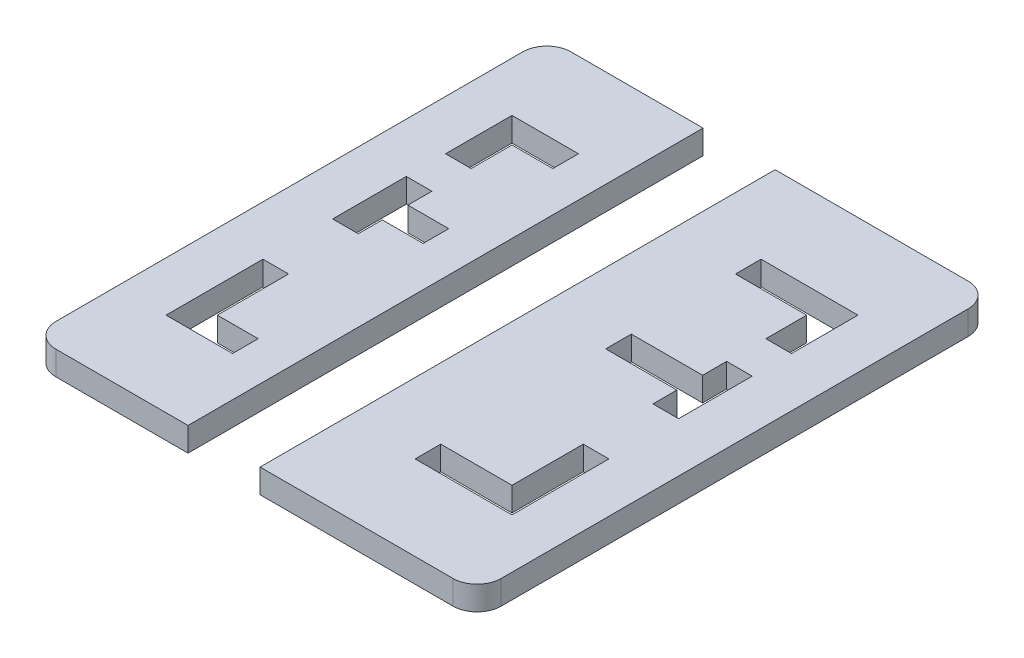
SolidWorks part; units mm, degrees
ref_plane "Front Plane" through (0, 0, 0) normal (0, 0, 1) x (1, 0, 0)
ref_plane "Top Plane" through (0, 0, 0) normal (0, 1, 0) x (1, 0, 0)
ref_plane "Right Plane" through (0, 0, 0) normal (1, 0, 0) x (0, 0, -1)
sketch "Sketch1" plane through (0, 0, 0) normal (0, 1, 0) x (1, 0, 0)
  line L0 (0.7, -32.157) -> (0.7, 32.157)
  line L1 (-28.5, -32.157) -> (28.5, -32.157) construction
  line L2 (-28.5, -32.157) -> (-28.5, 32.157) construction
  line L3 (-28.5, 32.157) -> (28.5, 32.157) construction
  line L4 (28.5, -32.157) -> (28.5, 32.157) construction
  line L5 (-8.3, 32.157) -> (-8.3, -32.157)
  line L6 (27.8, -32.157) -> (27.8, 32.157)
  line L7 (-27.8, -32.157) -> (-27.8, 32.157)
  line L8 (0, -32.157) -> (0, 32.157) construction
  line L9 (0.7, -32.157) -> (27.8, -32.157)
  line L10 (27.8, 32.157) -> (0.7, 32.157)
  line L11 (-8.3, 32.157) -> (-27.8, 32.157)
  line L12 (-8.3, -32.157) -> (-27.8, -32.157)
  line L13 (28.5, 0) -> (27.8, 0) construction
  line L14 (27.8, 20) -> (28.5, 20) construction
sketch "Sketch2" plane through (0, 0, 0) normal (0, 0, 1) x (1, 0, 0)
  line L0 (0.7, 0) -> (27.8, 0) construction
  line L1 (27.8, 0) -> (0.7, 0)
  line L2 (27.8, 0) -> (27.8, 3)
  line L3 (27.8, 3) -> (0.7, 3)
  line L4 (0.7, 0) -> (0.7, 3)
  line L5 (28.5, 3) -> (0.7, 3) construction
  line L7 (-8.3, 3) -> (-27.8, 3)
  line L8 (-8.3, 3) -> (-8.3, 0)
  line L9 (-8.3, 0) -> (-27.8, 0)
  line L10 (-27.8, 3) -> (-27.8, 0)
extrude "Boss-Extrude1" add sketch "Sketch1" along normal up to vertex (3 mm away) up to point (-27.8, 3, 0)
sketch "Sketch3" plane through (0, 0, 0) normal (0, 1, 0) x (1, 0, 0)
  line L0 (21.5, 2.3) -> (-21.5, 2.3) construction
  line L1 (21.5, -21.5) -> (-21.5, -21.5) construction
  line L2 (21.5, -21.5) -> (21.5, 21.5) construction
  line L3 (21.5, 21.5) -> (-21.5, 21.5) construction
  line L4 (-21.5, -21.5) -> (-21.5, 21.5) construction
  line L5 (18.5, -18.5) -> (-18.5, -18.5) construction
  line L6 (18.5, -18.5) -> (18.5, 18.5) construction
  line L7 (18.5, 18.5) -> (-18.5, 18.5) construction
  line L8 (-18.5, -18.5) -> (-18.5, 18.5) construction
  line L9 (-21.5, 5.3) -> (21.5, 5.3) construction
  line L10 (21.5, -0.7) -> (-21.5, -0.7) construction
  line L11 (21.5, 8.3) -> (-21.5, 8.3) construction
  line L12 (21.5, -9.6) -> (-21.5, -9.6) construction
  line L13 (21.5, 13.4) -> (-21.5, 13.4) construction
  line L14 (-13.4, -21.5) -> (-13.4, 21.5) construction
  line L15 (9.6, -21.5) -> (9.6, 21.5) construction
  line L16 (21.5, -21.5) -> (9.6, -21.5)
  line L17 (9.6, -21.5) -> (9.6, -18.5)
  line L18 (9.6, -18.5) -> (18.5, -18.5)
  line L19 (18.5, -18.5) -> (18.5, -9.6)
  line L20 (18.5, -9.6) -> (21.5, -9.6)
  line L21 (21.5, -9.6) -> (21.5, -21.5)
  line L22 (21.5, -0.7) -> (18.5, -0.7)
  line L23 (18.5, -0.7) -> (18.5, 2.3)
  line L24 (18.5, 2.3) -> (9.6, 2.3)
  line L25 (9.6, 2.3) -> (9.6, 5.3)
  line L26 (9.6, 5.3) -> (18.5, 5.3)
  line L27 (18.5, 5.3) -> (18.5, 8.3)
  line L28 (18.5, 8.3) -> (21.5, 8.3)
  line L29 (21.5, 8.3) -> (21.5, -0.7)
  line L30 (21.5, 13.4) -> (18.5, 13.4)
  line L31 (18.5, 13.4) -> (18.5, 18.5)
  line L32 (18.5, 18.5) -> (9.6, 18.5)
  line L33 (9.6, 18.5) -> (9.6, 21.5)
  line L34 (9.6, 21.5) -> (21.5, 21.5)
  line L35 (21.5, 21.5) -> (21.5, 13.4)
  line L36 (-13.4, 21.5) -> (-21.5, 21.5)
  line L37 (-21.5, 21.5) -> (-21.5, 13.4)
  line L38 (-21.5, 13.4) -> (-18.5, 13.4)
  line L39 (-18.5, 13.4) -> (-18.5, 18.5)
  line L40 (-18.5, 18.5) -> (-13.4, 18.5)
  line L41 (-13.4, 18.5) -> (-13.4, 21.5)
  line L42 (-21.5, -0.7) -> (-21.5, 8.3)
  line L43 (-21.5, 8.3) -> (-18.5, 8.3)
  line L44 (-18.5, 8.3) -> (-18.5, 5.3)
  line L45 (-18.5, 5.3) -> (-13.4, 5.3)
  line L46 (-13.4, 5.3) -> (-13.4, 2.3)
  line L47 (-13.4, 2.3) -> (-18.5, 2.3)
  line L48 (-18.5, 2.3) -> (-18.5, -0.7)
  line L49 (-18.5, -0.7) -> (-21.5, -0.7)
  line L51 (-21.5, -9.6) -> (-21.5, -21.5)
  line L52 (-21.5, -21.5) -> (-13.4, -21.5)
  line L53 (-13.4, -21.5) -> (-13.4, -18.5)
  line L54 (-13.4, -18.5) -> (-18.5, -18.5)
  line L55 (-18.5, -18.5) -> (-18.5, -9.6)
  line L56 (-18.5, -9.6) -> (-21.5, -9.6)
sketch "Sketch4" plane through (0, 0, 0) normal (0, 1, 0) x (1, 0, 0)
  line L0 (18.4, 2.2) -> (18.4, -0.8)
  line L1 (18.4, -0.8) -> (21.6, -0.8)
  line L2 (21.6, -0.8) -> (21.6, 8.4)
  line L3 (21.6, 8.4) -> (18.4, 8.4)
  line L4 (18.4, 8.4) -> (18.4, 5.4)
  line L5 (18.4, 5.4) -> (9.5, 5.4)
  line L6 (9.6, -18.5) -> (9.6, -21.5)
  line L7 (18.5, -18.5) -> (9.6, -18.5)
  line L8 (18.5, 2.3) -> (18.5, -0.7)
  line L9 (9.6, 2.3) -> (18.5, 2.3)
  line L10 (9.6, 5.3) -> (9.6, 2.3)
  line L11 (18.5, 5.3) -> (9.6, 5.3)
  line L12 (18.5, 8.3) -> (18.5, 5.3)
  line L13 (21.5, 8.3) -> (18.5, 8.3)
  line L14 (21.5, -0.7) -> (21.5, 8.3)
  line L15 (18.5, -0.7) -> (21.5, -0.7)
  line L16 (18.5, 2.3) -> (18.5, -0.7) construction
  line L17 (9.6, 2.3) -> (18.5, 2.3) construction
  line L18 (9.6, 5.3) -> (9.6, 2.3) construction
  line L19 (18.5, 5.3) -> (9.6, 5.3) construction
  line L20 (18.5, 8.3) -> (18.5, 5.3) construction
  line L21 (21.5, 8.3) -> (18.5, 8.3) construction
  line L22 (21.5, -0.7) -> (21.5, 8.3) construction
  line L23 (18.5, -0.7) -> (21.5, -0.7) construction
  line L24 (18.5, -9.6) -> (18.5, -18.5)
  line L25 (21.5, -9.6) -> (18.5, -9.6)
  line L26 (21.5, -21.5) -> (21.5, -9.6)
  line L27 (9.6, -21.5) -> (21.5, -21.5)
  line L28 (9.6, -18.5) -> (9.6, -21.5) construction
  line L29 (18.5, -18.5) -> (9.6, -18.5) construction
  line L30 (18.5, -9.6) -> (18.5, -18.5) construction
  line L31 (21.5, -9.6) -> (18.5, -9.6) construction
  line L32 (21.5, -21.5) -> (21.5, -9.6) construction
  line L33 (9.6, -21.5) -> (21.5, -21.5) construction
  line L34 (-13.4, -18.5) -> (-18.5, -18.5)
  line L35 (-18.5, -18.5) -> (-18.5, -9.6)
  line L36 (-18.5, -9.6) -> (-21.5, -9.6)
  line L37 (-21.5, -9.6) -> (-21.5, -21.5)
  line L38 (-21.5, -21.5) -> (-13.4, -21.5)
  line L39 (-13.4, -21.5) -> (-13.4, -18.5)
  line L40 (-13.4, -18.5) -> (-18.5, -18.5) construction
  line L41 (-18.5, -18.5) -> (-18.5, -9.6) construction
  line L42 (-18.5, -9.6) -> (-21.5, -9.6) construction
  line L43 (-21.5, -9.6) -> (-21.5, -21.5) construction
  line L44 (-21.5, -21.5) -> (-13.4, -21.5) construction
  line L45 (-13.4, -21.5) -> (-13.4, -18.5) construction
  line L46 (-18.5, 18.5) -> (-13.4, 18.5)
  line L47 (-18.5, 13.4) -> (-18.5, 18.5)
  line L48 (-18.5, 5.3) -> (-18.5, 8.3)
  line L49 (-13.4, 5.3) -> (-18.5, 5.3)
  line L50 (-13.4, 2.3) -> (-13.4, 5.3)
  line L51 (-18.5, 2.3) -> (-13.4, 2.3)
  line L52 (-18.5, -0.7) -> (-18.5, 2.3)
  line L53 (-21.5, -0.7) -> (-18.5, -0.7)
  line L54 (-21.5, 8.3) -> (-21.5, -0.7)
  line L55 (-18.5, 8.3) -> (-21.5, 8.3)
  line L56 (-18.5, 5.3) -> (-18.5, 8.3) construction
  line L57 (-13.4, 5.3) -> (-18.5, 5.3) construction
  line L58 (-13.4, 2.3) -> (-13.4, 5.3) construction
  line L59 (-18.5, 2.3) -> (-13.4, 2.3) construction
  line L60 (-18.5, -0.7) -> (-18.5, 2.3) construction
  line L61 (-21.5, -0.7) -> (-18.5, -0.7) construction
  line L62 (-21.5, 8.3) -> (-21.5, -0.7) construction
  line L63 (-18.5, 8.3) -> (-21.5, 8.3) construction
  line L64 (-21.5, 13.4) -> (-18.5, 13.4)
  line L65 (-21.5, 21.5) -> (-21.5, 13.4)
  line L66 (-13.4, 21.5) -> (-21.5, 21.5)
  line L67 (-13.4, 18.5) -> (-13.4, 21.5)
  line L68 (-18.5, 18.5) -> (-13.4, 18.5) construction
  line L69 (-18.5, 13.4) -> (-18.5, 18.5) construction
  line L70 (-21.5, 13.4) -> (-18.5, 13.4) construction
  line L71 (-21.5, 21.5) -> (-21.5, 13.4) construction
  line L72 (-13.4, 21.5) -> (-21.5, 21.5) construction
  line L73 (-13.4, 18.5) -> (-13.4, 21.5) construction
  line L74 (18.5, 18.5) -> (18.5, 13.4)
  line L75 (9.6, 18.5) -> (18.5, 18.5)
  line L76 (9.6, 21.5) -> (9.6, 18.5)
  line L77 (21.5, 21.5) -> (9.6, 21.5)
  line L78 (21.5, 13.4) -> (21.5, 21.5)
  line L79 (18.5, 13.4) -> (21.5, 13.4)
  line L80 (18.5, 18.5) -> (18.5, 13.4) construction
  line L81 (9.6, 18.5) -> (18.5, 18.5) construction
  line L82 (9.6, 21.5) -> (9.6, 18.5) construction
  line L83 (21.5, 21.5) -> (9.6, 21.5) construction
  line L84 (21.5, 13.4) -> (21.5, 21.5) construction
  line L85 (18.5, 13.4) -> (21.5, 13.4) construction
  line L86 (9.5, 5.4) -> (9.5, 2.2)
  line L87 (9.5, 2.2) -> (18.4, 2.2)
  line L88 (9.5, -18.4) -> (9.5, -21.6)
  line L89 (9.5, -21.6) -> (21.6, -21.6)
  line L90 (21.6, -21.6) -> (21.6, -9.5)
  line L91 (21.6, -9.5) -> (18.4, -9.5)
  line L92 (18.4, -9.5) -> (18.4, -18.4)
  line L93 (18.4, -18.4) -> (9.5, -18.4)
  line L94 (-13.3, -18.4) -> (-18.4, -18.4)
  line L95 (-18.4, -18.4) -> (-18.4, -9.5)
  line L96 (-18.4, -9.5) -> (-21.6, -9.5)
  line L97 (-21.6, -9.5) -> (-21.6, -21.6)
  line L98 (-21.6, -21.6) -> (-13.3, -21.6)
  line L99 (-13.3, -21.6) -> (-13.3, -18.4)
  line L100 (-18.4, 5.4) -> (-18.4, 8.4)
  line L101 (-18.4, 8.4) -> (-21.6, 8.4)
  line L102 (-21.6, 8.4) -> (-21.6, -0.8)
  line L103 (-21.6, -0.8) -> (-18.4, -0.8)
  line L104 (-18.4, -0.8) -> (-18.4, 2.2)
  line L105 (-18.4, 2.2) -> (-13.3, 2.2)
  line L106 (-13.3, 2.2) -> (-13.3, 5.4)
  line L107 (-13.3, 5.4) -> (-18.4, 5.4)
  line L108 (-18.4, 18.4) -> (-13.3, 18.4)
  line L109 (-13.3, 18.4) -> (-13.3, 21.6)
  line L110 (-13.3, 21.6) -> (-21.6, 21.6)
  line L111 (-21.6, 21.6) -> (-21.6, 13.3)
  line L112 (-21.6, 13.3) -> (-18.4, 13.3)
  line L113 (-18.4, 13.3) -> (-18.4, 18.4)
  line L114 (18.4, 18.4) -> (18.4, 13.3)
  line L115 (18.4, 13.3) -> (21.6, 13.3)
  line L116 (21.6, 13.3) -> (21.6, 21.6)
  line L117 (21.6, 21.6) -> (9.5, 21.6)
  line L118 (9.5, 21.6) -> (9.5, 18.4)
  line L119 (9.5, 18.4) -> (18.4, 18.4)
  dimension "D1" = 0
  dimension "D2" = 0
  dimension "D3" = 0
  dimension "D4" = 0
  dimension "D5" = 0
  dimension "D6" = 0
  dimension "D7" = 0.1
extrude "Cut-Extrude1" cut sketch "Sketch4" along normal through all
fillet "Fillet1" radius 3 2 edges at (27.8, 1.5, 32.157) (27.8, 1.5, -32.157)
fillet "Fillet2" radius 3 2 edges at (-27.8, 1.5, -32.157) (-27.8, 1.5, 32.157)
